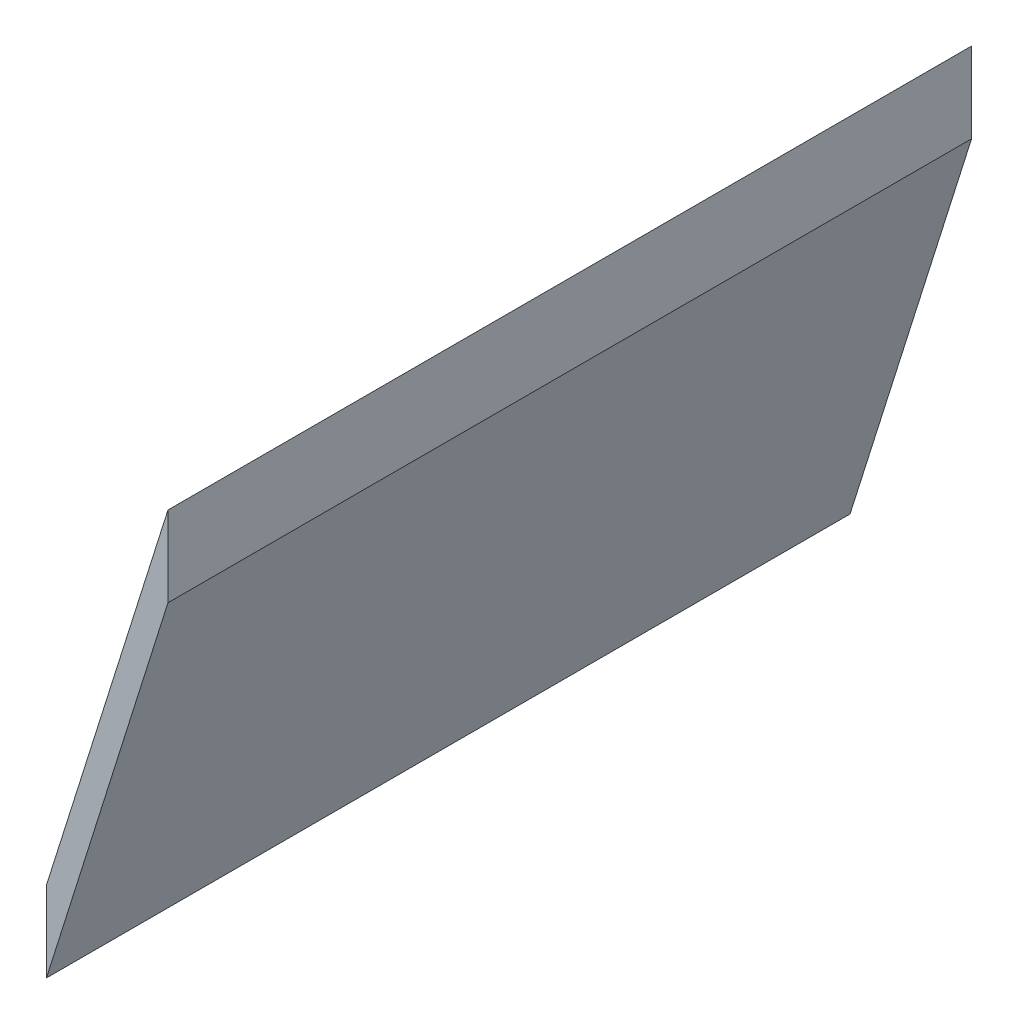
SolidWorks part; units mm, degrees
ref_plane "Front Plane" through (0, 0, 0) normal (0, 0, 1) x (1, 0, 0)
ref_plane "Top Plane" through (0, 0, 0) normal (0, 1, 0) x (1, 0, 0)
ref_plane "Right Plane" through (0, 0, 0) normal (1, 0, 0) x (0, 0, -1)
sketch "Sketch1" plane through (0, 0, 0) normal (0, 0, 1) x (1, 0, 0)
  line L12 (15.8431, 44.9495) -> (15.8431, 34.9495)
  line L13 (15.8431, 34.9495) -> (0.718, -13.0505)
  line L14 (0.718, -13.0505) -> (0.718, -3.0505)
  line L15 (0.718, -3.0505) -> (15.8431, 44.9495)
  dimension "D1" = 10
  dimension "D2" = 48
  dimension "D3" = 197.49
extrude "Boss-Extrude1" add sketch "Sketch1" along normal mid plane 100
